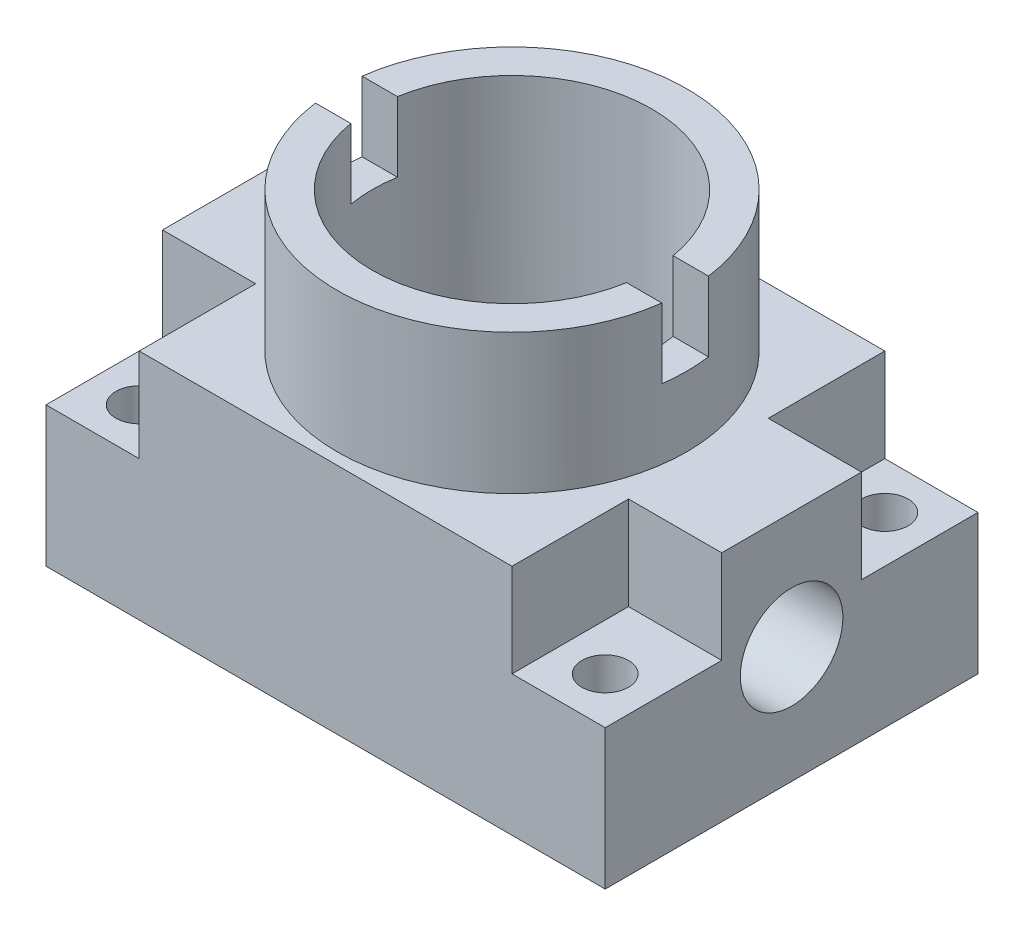
SolidWorks part; units mm, degrees
ref_plane "Спереди" through (0, 0, 0) normal (0, 0, 1) x (1, 0, 0)
ref_plane "Сверху" through (0, 0, 0) normal (0, 1, 0) x (1, 0, 0)
ref_plane "Справа" through (0, 0, 0) normal (1, 0, 0) x (0, 0, -1)
sketch "Эскиз1" plane through (0, 0, 0) normal (0, 1, 0) x (1, 0, 0)
  line L1 (60, -40) -> (-60, -40)
  line L2 (60, -40) -> (60, 40)
  line L3 (60, 40) -> (-60, 40)
  line L4 (-60, -40) -> (-60, 40)
  line L5 (60, -40) -> (-60, 40) construction
  line L6 (60, 40) -> (-60, -40) construction
  point P0 (0, 0)
  dimension "D1" = 120
  dimension "D2" = 80
extrude "Бобышка-Вытянуть1" add sketch "Эскиз1" along normal blind 50
sketch "Эскиз2" plane through (0, 50, 0) normal (0, 1, 0) x (1, 0, 0)
  line L0 (0, 0) -> (-60, 0) construction
  line L1 (-60, 40) -> (-60, -40) construction
  line L2 (0, 0) -> (0, 40) construction
  line L3 (60, 40) -> (-60, 40) construction
  line L4 (-60, 15) -> (-40, 15)
  line L5 (-40, 15) -> (-40, 40)
  line L6 (-60, 15) -> (-60, 40)
  line L7 (-60, 40) -> (-40, 40)
  line L8 (-60, -15) -> (-60, -40)
  line L9 (-60, -15) -> (-40, -15)
  line L10 (-40, -15) -> (-40, -40)
  line L11 (-60, -40) -> (-40, -40)
  line L12 (60, -15) -> (40, -15)
  line L13 (40, -15) -> (40, -40)
  line L14 (60, -40) -> (40, -40)
  line L15 (60, -15) -> (60, -40)
  line L16 (60, 15) -> (60, 40)
  line L17 (60, 15) -> (40, 15)
  line L18 (40, 15) -> (40, 40)
  line L19 (60, 40) -> (40, 40)
  dimension "D1" = 15
  dimension "D2" = 20
extrude "Вырез-Вытянуть1" cut sketch "Эскиз2" against normal blind 20
sketch "Эскиз3" plane through (0, 30, 0) normal (0, 1, 0) x (1, 0, 0)
  line L0 (0, 0) -> (-60, 0) construction
  line L1 (-60, 15) -> (-60, -15) construction
  line L2 (0, 40) -> (0, -40) construction
  line L3 (-40, -40) -> (40, -40) construction
  circle A0 centre (-50, -30) radius 5
  circle A1 centre (-50, 30) radius 5
  circle A2 centre (50, 30) radius 5
  circle A3 centre (50, -30) radius 5
  dimension "D1" = 10
  dimension "D2" = 50
  dimension "D3" = 30
extrude "Вырез-Вытянуть2" cut sketch "Эскиз3" against normal blind 30
sketch "Эскиз5" plane through (-60, 0, 0) normal (-1, 0, 0) x (0, 0, 1)
  line L0 (-40, 30) -> (-40, 0) construction
  line L1 (-15, 50) -> (15, 50) construction
  circle A0 centre (0, 25) radius 11
  dimension "D3" = 22
  dimension "D1" = 40
  dimension "D2" = 25
extrude "Вырез-Вытянуть4" cut sketch "Эскиз5" against normal blind 120
sketch "Эскиз6" plane through (0, 50, 0) normal (0, 1, 0) x (1, 0, 0)
  circle A0 centre (0, 0) radius 37.5
  dimension "D1" = 75
extrude "Бобышка-Вытянуть2" add sketch "Эскиз6" along normal blind 30
sketch "Эскиз7" plane through (0, 80, 0) normal (0, 1, 0) x (1, 0, 0)
  circle A0 centre (0, 0) radius 30
  dimension "D1" = 60
extrude "Вырез-Вытянуть5" cut sketch "Эскиз7" against normal through all
sketch "Эскиз8" plane through (0, 80, 0) normal (0, 1, 0) x (1, 0, 0)
  line L0 (0, 0) -> (-37.5, 0) construction
  line L1 (0, 0) -> (0, -37.5) construction
  line L2 (-29.5804, -5) -> (-37.1652, -5)
  line L3 (-37.1652, 5) -> (-29.5804, 5)
  line L4 (37.1652, 5) -> (29.5804, 5)
  line L5 (29.5804, -5) -> (37.1652, -5)
  circle A0 centre (0, 0) radius 37.5 construction
  circle A1 centre (0, 0) radius 37.5 construction
  arc A2 (-29.5804, 5) -> (-29.5804, -5) centre (0, 0) ccw
  arc A3 (-37.1652, 5) -> (-37.1652, -5) centre (0, 0) ccw
  arc A4 (29.5804, 5) -> (29.5804, -5) centre (0, 0) cw
  arc A5 (37.1652, 5) -> (37.1652, -5) centre (0, 0) cw
  dimension "D1" = 30
  dimension "D2" = 5
  dimension "D3" = 5
extrude "Вырез-Вытянуть6" cut sketch "Эскиз8" against normal blind 15
